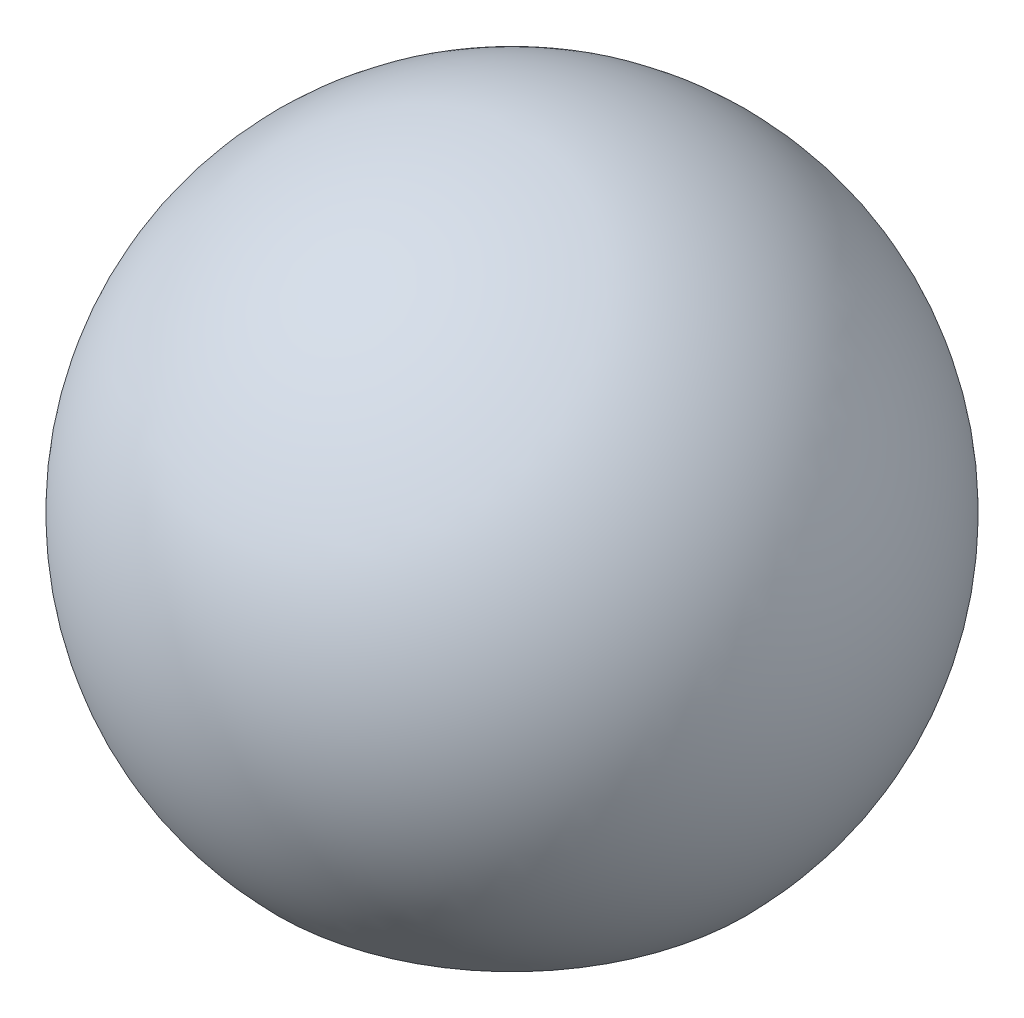
SolidWorks part; units mm, degrees
ref_plane "Front Plane" through (0, 0, 0) normal (0, 0, 1) x (1, 0, 0)
ref_plane "Top Plane" through (0, 0, 0) normal (0, 1, 0) x (1, 0, 0)
ref_plane "Right Plane" through (0, 0, 0) normal (1, 0, 0) x (0, 0, -1)
sketch "Sketch2" plane through (0, 0, 0) normal (0, 0, 1) x (1, 0, 0)
  line L0 (0, 1129.3635) -> (0, 0) construction
  line L2 (0, 900) -> (0, 1100)
  line L3 (284.1709, 218.4917) -> (426.2563, 77.7376)
  arc A0 (0, 900) -> (284.1709, 218.4917) centre (0, 500) cw
  arc A1 (0, 1100) -> (426.2563, 77.7376) centre (0, 500) cw
  dimension "D3" = 200
  dimension "D4" = 200
revolve "Revolve1" add sketch "Sketch2" angle 360 about L0
